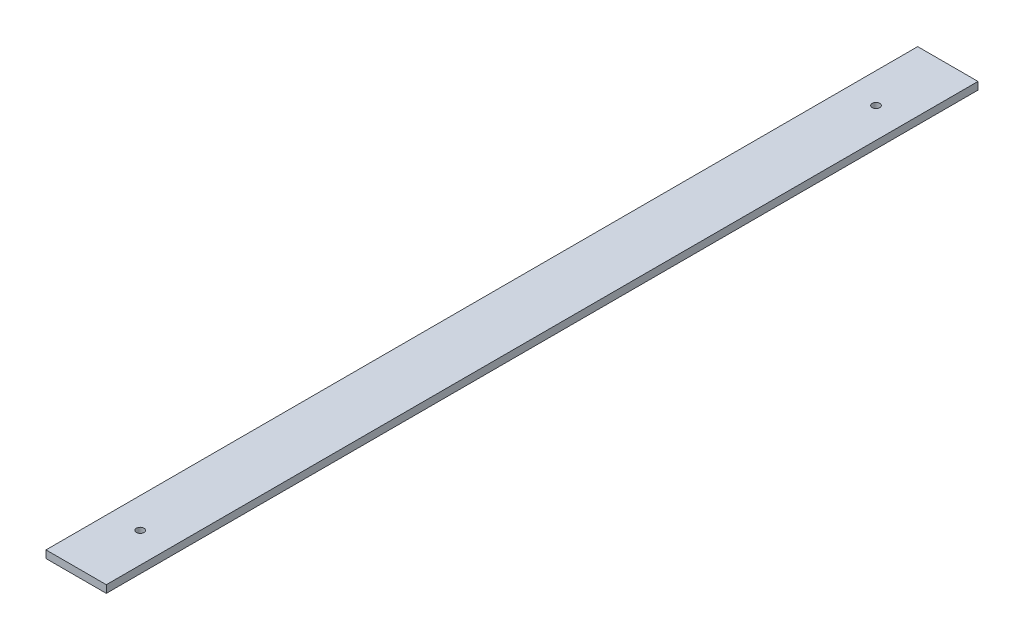
SolidWorks part; units mm, degrees
material "6063-O"
ref_plane "Front Plane" through (0, 0, 0) normal (0, 0, 1) x (1, 0, 0)
ref_plane "Top Plane" through (0, 0, 0) normal (0, 1, 0) x (1, 0, 0)
ref_plane "Right Plane" through (0, 0, 0) normal (1, 0, 0) x (0, 0, -1)
sketch "Sketch4" plane through (0, 0, 0) normal (0, 1, 0) x (1, 0, 0)
  line L4 (23232.9446, -10111.0305) -> (23232.9446, -10251.0305) construction
  line L5 (23232.9446, -9942.5829) -> (23032.9446, -9942.5829)
  line L6 (23232.9446, -9942.5829) -> (23232.9446, -12876.1567)
  line L7 (23232.9446, -12876.1567) -> (23032.9446, -12876.1567)
  line L8 (23032.9446, -9942.5829) -> (23032.9446, -12876.1567)
  line L9 (22132.9446, -9942.5829) -> (21932.9446, -9942.5829)
  line L10 (22132.9446, -9942.5829) -> (22132.9446, -12833.5838)
  line L11 (22132.9446, -12833.5838) -> (21932.9446, -12833.5838)
  line L12 (21932.9446, -9942.5829) -> (21932.9446, -12833.5838)
  line L13 (20932.9446, -9942.5829) -> (20732.9446, -9942.5829)
  line L14 (20932.9446, -9942.5829) -> (20932.9446, -12599.4325)
  line L15 (20932.9446, -12599.4325) -> (20732.9446, -12599.4325)
  line L16 (20732.9446, -9942.5829) -> (20732.9446, -12599.4325)
  line L17 (19732.9446, -9942.5829) -> (19532.9446, -9942.5829)
  line L18 (19732.9446, -9942.5829) -> (19732.9446, -12109.8436)
  line L19 (19732.9446, -12109.8436) -> (19532.9446, -12109.8436)
  line L20 (19532.9446, -9942.5829) -> (19532.9446, -12109.8436)
  line L21 (18902.9446, -9942.5829) -> (18702.9446, -9942.5829)
  line L22 (18902.9446, -9942.5829) -> (18902.9446, -11636.2195)
  line L23 (18902.9446, -11636.2195) -> (18702.9446, -11636.2195)
  line L24 (18702.9446, -9942.5829) -> (18702.9446, -11636.2195)
  line L25 (18702.9446, -10111.0305) -> (18702.9446, -10251.0305) construction
  line L26 (23132.9446, -12748.1199) -> (23132.9446, -12608.0593) construction
  line L27 (22032.9446, -12550.6075) -> (22032.9446, -12691.8491) construction
  line L28 (20832.9446, -12422.3488) -> (20832.9446, -12275.1597) construction
  line L29 (19632.9446, -11906.9658) -> (19632.9446, -11746.8651) construction
  line L30 (18802.9446, -11371.765) -> (18802.9446, -11195.5746) construction
  line L31 (23132.9446, -10251.0305) -> (23132.9446, -10111.0305) construction
  line L32 (18702.9446, -10251.0305) -> (23232.9446, -10251.0305) construction
  line L33 (23232.9446, -10111.0305) -> (18702.9446, -10111.0305) construction
  circle A0 centre (23132.9446, -12678.0896) radius 12.5
  arc A1 (18702.9446, -11295.1434) -> (23232.9446, -12744.4799) centre (22932.9446, -5878.0705) ccw construction
  arc A2 (18702.9446, -11116.3765) -> (23232.9446, -12604.3436) centre (22932.9446, -5878.0705) ccw construction
  circle A3 centre (22032.9446, -12621.2283) radius 12.5
  circle A4 centre (20832.9446, -12348.7542) radius 12.5
  circle A5 centre (19632.9446, -11826.9154) radius 12.5
  circle A6 centre (18802.9446, -11283.6698) radius 12.5
  circle A7 centre (18802.9446, -10181.0305) radius 12.5
  circle A8 centre (19632.9446, -10181.0305) radius 12.5
  circle A9 centre (20832.9446, -10181.0305) radius 12.5
  circle A10 centre (22032.9446, -10181.0305) radius 12.5
  circle A11 centre (23132.9446, -10181.0305) radius 12.5
  arc A12 (18702.9446, -11116.3765) -> (23232.9446, -12604.3436) centre (22932.9446, -5878.0705) ccw construction
  point P22 (23132.9446, -9942.5829)
  point P23 (22032.9446, -9942.5829)
  point P24 (20832.9446, -9942.5829)
  point P25 (19632.9446, -9942.5829)
  point P26 (23132.9446, -12876.1567)
  point P30 (20832.9446, -12599.4325)
  point P40 (23132.9446, -12678.0896)
  point P59 (22032.9446, -12621.2283)
  point P60 (22032.9446, -12833.5838)
  point P68 (20832.9446, -12348.7542)
  point P69 (19632.9446, -12109.8436)
  point P73 (19632.9446, -11826.9154)
  point P74 (18802.9446, -11283.6698)
  point P75 (18802.9446, -11636.2195)
  point P78 (23132.9446, -10181.0305)
  point P91 (18802.9446, -9942.5829)
  dimension "D5" = 25
  dimension "D1" = 200
  dimension "D2" = 1200
  dimension "D3" = 1200
  dimension "D4" = 1200
  dimension "D6" = 100
  dimension "D7" = 70
extrude "Boss-Extrude1" add sketch "Sketch4" along normal blind 25
sketch "Sketch5" plane through (0, 0, 0) normal (0, 1, 0) x (1, 0, 0)
  line L1 (21479.0733, -13339.3209) -> (16984.6666, -13339.3209)
  line L2 (21479.0733, -13339.3209) -> (21479.0733, -8598.1625)
  line L3 (21479.0733, -8598.1625) -> (16984.6666, -8598.1625)
  line L4 (16984.6666, -13339.3209) -> (16984.6666, -8598.1625)
  line L5 (24581.0951, -14678.8304) -> (22607.0812, -14678.8304)
  line L6 (24581.0951, -14678.8304) -> (24581.0951, -8210.4098)
  line L7 (24581.0951, -8210.4098) -> (22607.0812, -8210.4098)
  line L8 (22607.0812, -14678.8304) -> (22607.0812, -8210.4098)
extrude "Cut-Extrude1" cut sketch "Sketch5" along normal blind 10
sketch "Sketch6" plane through (0, 0, 0) normal (0, 1, 0) x (1, 0, 0)
  line L1 (21399.413, -9480.4004) -> (17886.4353, -9480.4004)
  line L2 (21399.413, -9480.4004) -> (21399.413, -13207.4715)
  line L3 (21399.413, -13207.4715) -> (17886.4353, -13207.4715)
  line L4 (17886.4353, -9480.4004) -> (17886.4353, -13207.4715)
  line L5 (22622.4341, -13300.8688) -> (23769.1713, -13300.8688)
  line L6 (22622.4341, -13300.8688) -> (22622.4341, -8706.6008)
  line L7 (22622.4341, -8706.6008) -> (23769.1713, -8706.6008)
  line L8 (23769.1713, -13300.8688) -> (23769.1713, -8706.6008)
extrude "Cut-Extrude2" cut sketch "Sketch6" along normal through all
